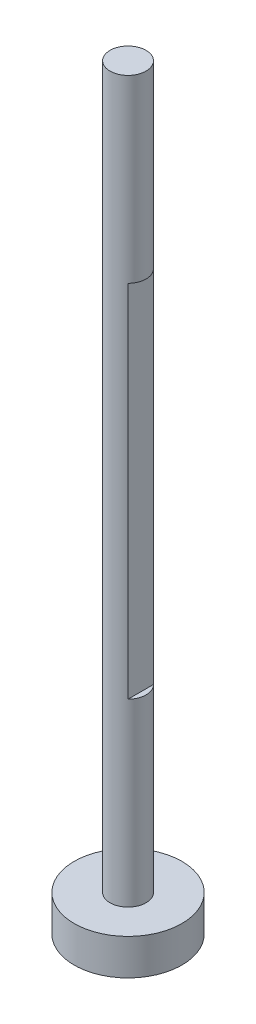
SolidWorks part; units mm, degrees
ref_plane "Front Plane" through (0, 0, 0) normal (0, 0, 1) x (1, 0, 0)
ref_plane "Top Plane" through (0, 0, 0) normal (0, 1, 0) x (1, 0, 0)
ref_plane "Right Plane" through (0, 0, 0) normal (1, 0, 0) x (0, 0, -1)
sketch "Sketch1" plane through (0, 0, 0) normal (0, 1, 0) x (1, 0, 0)
  circle A0 centre (0, 0) radius 3.175
  dimension "D1" = 6.35
extrude "Boss-Extrude1" add sketch "Sketch1" along normal blind 127
sketch "Sketch2" plane through (0, 0, 0) normal (0, -1, 0) x (1, 0, 0)
  line L0 (0, 0) -> (2.2451, 2.2451) construction
  line L1 (0, 0) -> (2.2451, -2.2451) construction
  line L2 (2.2451, 2.2451) -> (2.2451, -2.2451)
  line L3 (2.2451, 2.2451) -> (3.3629, 2.2451)
  line L4 (3.3629, 2.2451) -> (3.3629, -2.2451)
  line L5 (3.3629, -2.2451) -> (2.2451, -2.2451)
  circle A0 centre (0, 0) radius 3.175 construction
  circle A1 centre (0, 0) radius 3.175 construction
  dimension "D1" = 3.175
extrude "Cut-Extrude1" cut sketch "Sketch2" against normal blind 63.5 from offset 31.75 offset against normal yes
sketch "Sketch3" plane through (0, 0, 0) normal (0, -1, 0) x (1, 0, 0)
  circle A0 centre (0, 0) radius 9.5
  dimension "D1" = 19
extrude "Boss-Extrude2" add sketch "Sketch3" along normal blind 6.35
